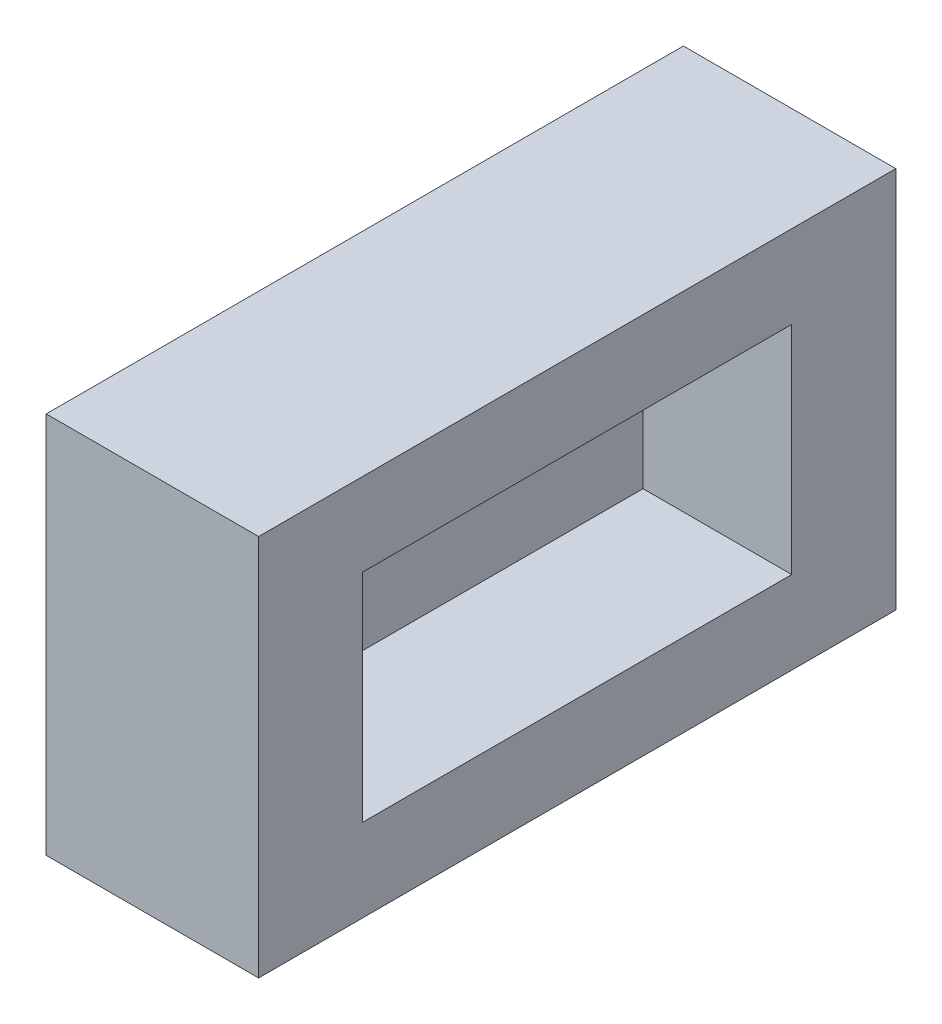
SolidWorks part; units mm, degrees
ref_plane "Спереди" through (0, 0, 0) normal (0, 0, 1) x (1, 0, 0)
ref_plane "Сверху" through (0, 0, 0) normal (0, 1, 0) x (1, 0, 0)
ref_plane "Справа" through (0, 0, 0) normal (1, 0, 0) x (0, 0, -1)
sketch "Sketch1" plane through (0, 0, 0) normal (0, 1, 0) x (1, 0, 0)
  line L1 (5, -15) -> (-5, -15)
  line L2 (5, -15) -> (5, 15)
  line L3 (5, 15) -> (-5, 15)
  line L4 (-5, -15) -> (-5, 15)
  line L5 (5, -15) -> (-5, 15) construction
  line L6 (5, 15) -> (-5, -15) construction
  point P0 (0, 0)
  dimension "D1" = 10
  dimension "D2" = 30
extrude "Boss-Extrude1" add sketch "Sketch1" along normal blind 18
sketch "Sketch2" plane through (5, 0, 0) normal (1, 0, 0) x (0, 0, -1)
  line L0 (15, 9) -> (-15, 9) construction
  line L1 (15, 18) -> (15, 0) construction
  line L2 (-15, 18) -> (-15, 0) construction
  line L4 (-10.1, 3.9) -> (10.1, 3.9)
  line L5 (-10.1, 3.9) -> (-10.1, 14.1)
  line L6 (-10.1, 14.1) -> (10.1, 14.1)
  line L7 (10.1, 3.9) -> (10.1, 14.1)
  line L8 (-10.1, 3.9) -> (10.1, 14.1) construction
  line L9 (-10.1, 14.1) -> (10.1, 3.9) construction
  point P6 (0, 9)
  dimension "D1" = 10.2
  dimension "D2" = 20.2
extrude "Cut-Extrude1" cut sketch "Sketch2" against normal blind 7
